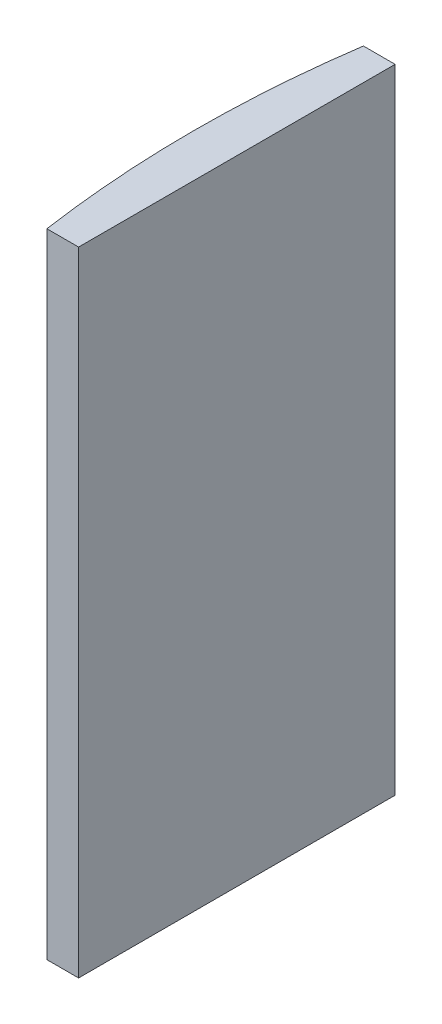
SolidWorks part; units mm, degrees
ref_plane "前视基准面" through (0, 0, 0) normal (0, 0, 1) x (1, 0, 0)
ref_plane "上视基准面" through (0, 0, 0) normal (0, 1, 0) x (1, 0, 0)
ref_plane "右视基准面" through (0, 0, 0) normal (1, 0, 0) x (0, 0, -1)
sketch "草图1" plane through (0, 0, 0) normal (0, 1, 0) x (1, 0, 0)
  line L0 (10.7432, 0) -> (-607.0701, 0) construction
  line L1 (-97.951, 15) -> (-94.9448, 15)
  line L2 (-97.951, -15) -> (-94.9448, -15)
  line L3 (-94.9448, 15) -> (-94.9448, -15)
  arc A0 (-97.951, 15) -> (-97.951, -15) centre (4.3552, 0) ccw
  point P19 (-99.0448, 0)
  point P20 (-94.9448, 0)
  dimension "D2" = 15
  dimension "D3" = 103.4
  dimension "D4" = 4.1
  dimension "D1" = 15
extrude "凸台-拉伸1" add sketch "草图1" along normal blind 60
